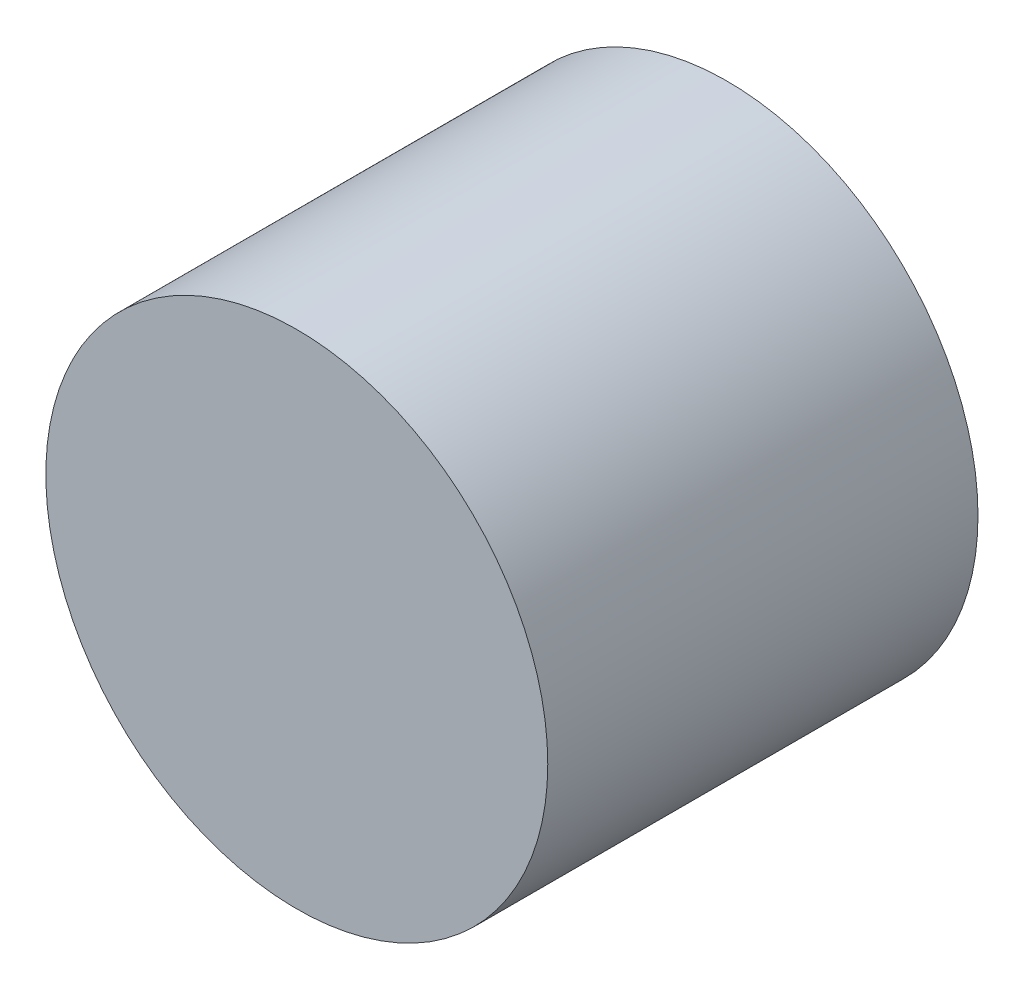
SolidWorks part; units mm, degrees
ref_plane "Piano frontale" through (0, 0, 0) normal (0, 0, 1) x (1, 0, 0)
ref_plane "Piano superiore" through (0, 0, 0) normal (0, 1, 0) x (1, 0, 0)
ref_plane "Piano destro" through (0, 0, 0) normal (1, 0, 0) x (0, 0, -1)
sketch "Schizzo1" plane through (0, 0, 0) normal (0, 0, 1) x (1, 0, 0)
  circle A0 centre (0, 0) radius 1.75
  dimension "D1" = 3.5
extrude "Estrusione-Estrusione1" add sketch "Schizzo1" along normal blind 3 contours A0
